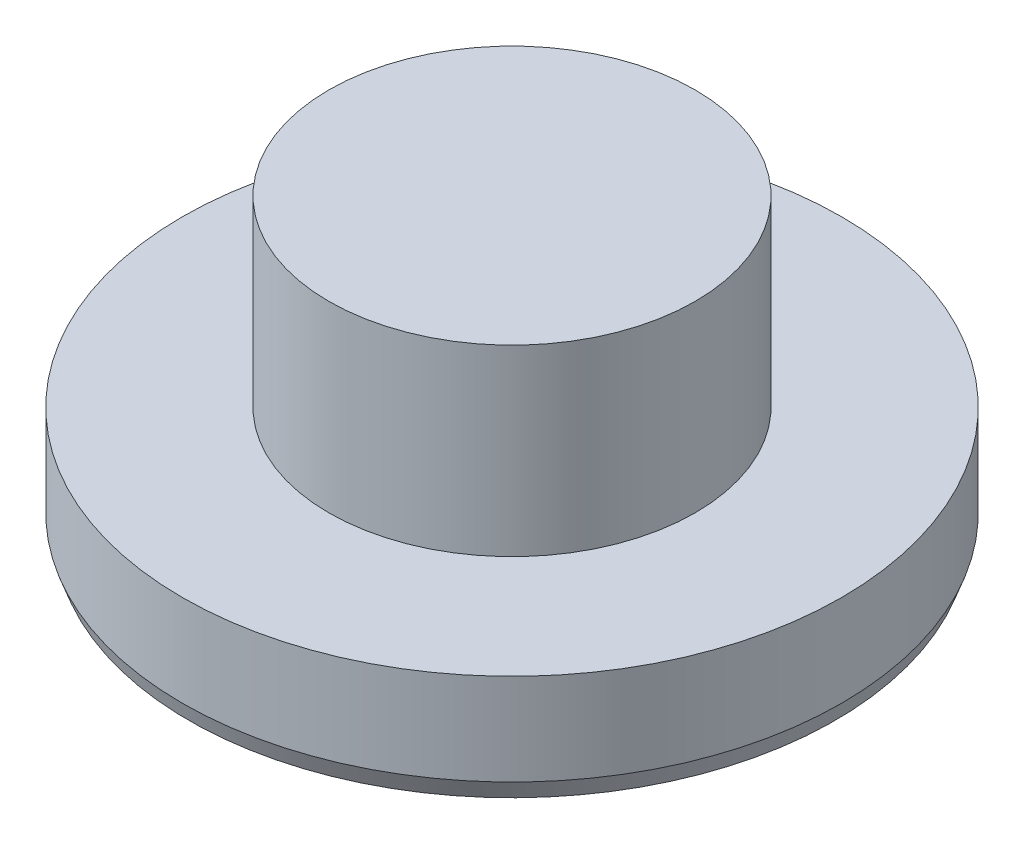
SolidWorks part; units mm, degrees
ref_plane "Спереди" through (0, 0, 0) normal (0, 0, 1) x (1, 0, 0)
ref_plane "Сверху" through (0, 0, 0) normal (0, 1, 0) x (1, 0, 0)
ref_plane "Справа" through (0, 0, 0) normal (1, 0, 0) x (0, 0, -1)
sketch "Эскиз1" plane through (0, 0, 0) normal (0, 0, 1) x (1, 0, 0)
  line L0 (0, 0) -> (0, 5)
  line L1 (0, 5) -> (5, 5)
  line L2 (5, 5) -> (5, 0)
  line L4 (5, 0) -> (9, 0)
  line L5 (9, 0) -> (9, -3)
  line L6 (9, -3) -> (0, -3)
  line L7 (0, -3) -> (0, 0)
  dimension "D1" = 5
  dimension "D2" = 5
  dimension "D3" = 4
  dimension "D4" = 3
revolve "Повернуть1" add sketch "Эскиз1" angle 360 about L0
sketch "Эскиз3" plane through (0, -3, 0) normal (0, -1, 0) x (1, 0, 0)
  circle A0 centre (0, 0) radius 6
  dimension "D1" = 12
extrude "Вырез-Вытянуть1" cut sketch "Эскиз3" against normal blind 1
chamfer "Фаска1" distance 1 angle 20 1 edges at (0, -3, -6)
chamfer "Фаска2" distance 0.5 angle 20 1 edges at (0, -3, -9)
